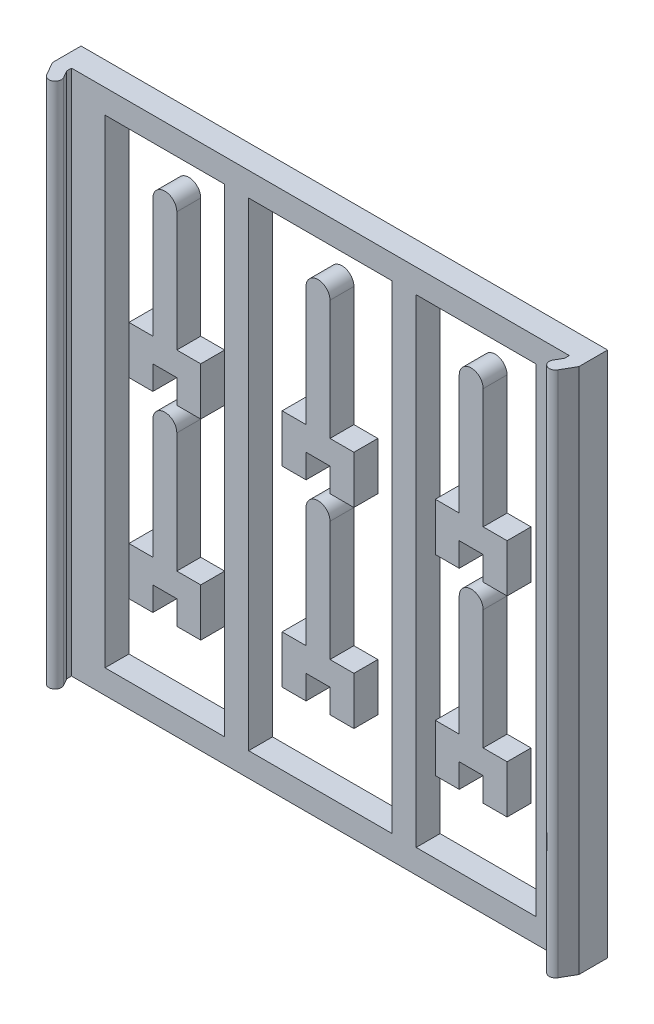
SolidWorks part; units mm, degrees
ref_plane "Front Plane" through (0, 0, 0) normal (0, 0, 1) x (1, 0, 0)
ref_plane "Top Plane" through (0, 0, 0) normal (0, 1, 0) x (1, 0, 0)
ref_plane "Right Plane" through (0, 0, 0) normal (1, 0, 0) x (0, 0, -1)
sketch "Sketch1" plane through (0, 0, 0) normal (0, 0, 1) x (1, 0, 0)
  line L0 (35, 105) -> (35, 5)
  line L1 (0, 0) -> (110, 0)
  line L2 (0, 0) -> (0, 110)
  line L3 (0, 110) -> (110, 110)
  line L4 (110, 0) -> (110, 110)
  line L5 (10, 5) -> (35, 5)
  line L6 (10, 5) -> (10, 105)
  line L7 (10, 105) -> (35, 105)
  line L8 (100, 5) -> (100, 105)
  line L9 (40, 105) -> (40, 5)
  line L10 (70, 105) -> (70, 5)
  line L11 (75, 105) -> (75, 5)
  line L12 (40, 105) -> (70, 105)
  line L13 (75, 105) -> (100, 105)
  line L14 (75, 5) -> (100, 5)
  line L15 (40, 5) -> (70, 5)
  dimension "D1" = 110
  dimension "D2" = 110
  dimension "D3" = 5
  dimension "D4" = 5
  dimension "D5" = 10
  dimension "D6" = 10
  dimension "D7" = 25
  dimension "D8" = 25
  dimension "D9" = 5
  dimension "D10" = 5
extrude "Boss-Extrude1" add sketch "Sketch1" along normal blind 5
sketch "Sketch2" plane through (0, 0, 0) normal (0, -1, 0) x (1, 0, 0)
  line L0 (0, 5) -> (3, 5)
  line L1 (0, 5) -> (110, 5) construction
  line L2 (3, 5) -> (3, 6)
  line L3 (3, 6) -> (3.866, 7.5)
  line L4 (55, 5) -> (55, 37.8918) construction
  line L5 (110, 6) -> (110, 5)
  line L6 (1.616, 8.799) -> (0, 6)
  line L7 (0, 6) -> (0, 5)
  line L8 (108.384, 8.799) -> (110, 6)
  line L9 (107, 6) -> (106.134, 7.5)
  line L10 (107, 5) -> (107, 6)
  line L11 (110, 5) -> (107, 5)
  arc A0 (3.866, 7.5) -> (1.616, 8.799) centre (2.741, 8.1495) ccw
  arc A1 (106.134, 7.5) -> (108.384, 8.799) centre (107.259, 8.1495) cw
  dimension "D1" = 3
  dimension "D2" = 1
  dimension "D3" = 2.5
  dimension "D4" = 1
  dimension "D5" = 30
extrude "Boss-Extrude2" add sketch "Sketch2" against normal blind 110
sketch "Sketch3" plane through (0, 0, 0) normal (0, 0, 1) x (1, 0, 0)
  line L1 (35, 105) -> (10, 105) construction
  line L2 (20, 95) -> (20, 70)
  line L3 (20, 65) -> (25, 65)
  line L4 (25, 95) -> (25, 70)
  line L5 (20, 70) -> (15, 70)
  line L6 (20, 65) -> (20, 60)
  line L7 (20, 60) -> (15, 60)
  line L8 (15, 70) -> (15, 60)
  line L9 (25, 70) -> (30, 70)
  line L10 (25, 65) -> (25, 60)
  line L11 (25, 60) -> (30, 60)
  line L12 (30, 70) -> (30, 60)
  line L13 (10, 105) -> (10, 5) construction
  line L14 (52, 95) -> (52, 70)
  line L15 (52, 65) -> (57, 65)
  line L16 (57, 95) -> (57, 70)
  line L17 (52, 70) -> (47, 70)
  line L18 (52, 65) -> (52, 60)
  line L19 (52, 60) -> (47, 60)
  line L20 (47, 70) -> (47, 60)
  line L21 (57, 70) -> (62, 70)
  line L22 (57, 65) -> (57, 60)
  line L23 (57, 60) -> (62, 60)
  line L24 (62, 70) -> (62, 60)
  line L25 (84, 95) -> (84, 70)
  line L26 (84, 65) -> (89, 65)
  line L27 (89, 95) -> (89, 70)
  line L28 (84, 70) -> (79, 70)
  line L29 (84, 65) -> (84, 60)
  line L30 (84, 60) -> (79, 60)
  line L31 (79, 70) -> (79, 60)
  line L32 (89, 70) -> (94, 70)
  line L33 (89, 65) -> (89, 60)
  line L34 (89, 60) -> (94, 60)
  line L35 (94, 70) -> (94, 60)
  line L36 (52, 55) -> (52, 30)
  line L37 (52, 25) -> (57, 25)
  line L38 (57, 55) -> (57, 30)
  line L39 (52, 30) -> (47, 30)
  line L40 (52, 25) -> (52, 20)
  line L41 (52, 20) -> (47, 20)
  line L42 (47, 30) -> (47, 20)
  line L43 (57, 30) -> (62, 30)
  line L44 (57, 25) -> (57, 20)
  line L45 (57, 20) -> (62, 20)
  line L46 (62, 30) -> (62, 20)
  line L47 (84, 55) -> (84, 30)
  line L48 (84, 25) -> (89, 25)
  line L49 (89, 55) -> (89, 30)
  line L50 (84, 30) -> (79, 30)
  line L51 (84, 25) -> (84, 20)
  line L52 (84, 20) -> (79, 20)
  line L53 (79, 30) -> (79, 20)
  line L54 (89, 30) -> (94, 30)
  line L55 (89, 25) -> (89, 20)
  line L56 (89, 20) -> (94, 20)
  line L57 (94, 30) -> (94, 20)
  line L58 (20, 55) -> (20, 30)
  line L59 (20, 25) -> (25, 25)
  line L60 (25, 55) -> (25, 30)
  line L61 (20, 30) -> (15, 30)
  line L62 (20, 25) -> (20, 20)
  line L63 (20, 20) -> (15, 20)
  line L64 (15, 30) -> (15, 20)
  line L65 (25, 30) -> (30, 30)
  line L66 (25, 25) -> (25, 20)
  line L67 (25, 20) -> (30, 20)
  line L68 (30, 30) -> (30, 20)
  arc A0 (20, 95) -> (25, 95) centre (22.5, 95) cw
  arc A1 (52, 95) -> (57, 95) centre (54.5, 95) cw
  arc A2 (84, 95) -> (89, 95) centre (86.5, 95) cw
  arc A3 (52, 55) -> (57, 55) centre (54.5, 55) cw
  arc A4 (84, 55) -> (89, 55) centre (86.5, 55) cw
  arc A5 (20, 55) -> (25, 55) centre (22.5, 55) cw
  dimension "D10" = 25
  dimension "D1" = 30
  dimension "D2" = 5
  dimension "D3" = 5
  dimension "D4" = 5
  dimension "D5" = 5
  dimension "D6" = 10
  dimension "D7" = 10
  dimension "D8" = 5
  dimension "D9" = 5
  dimension "D11" = 3
  dimension "D12" = 2
extrude "Boss-Extrude3" add sketch "Sketch3" along normal blind 5 separate body
